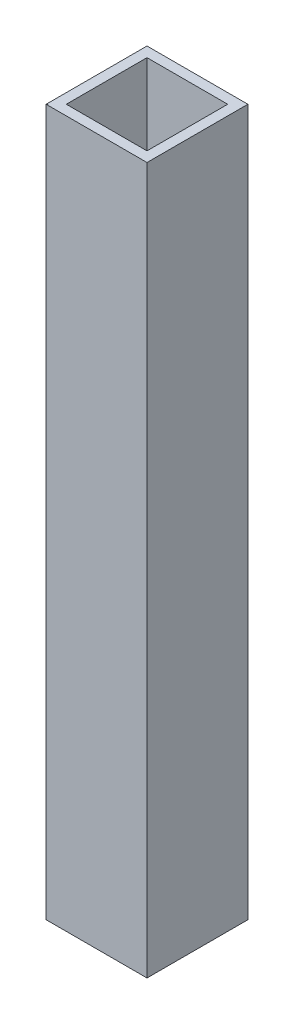
SolidWorks part; units mm, degrees
ref_plane "前视基准面" through (0, 0, 0) normal (0, 0, 1) x (1, 0, 0)
ref_plane "上视基准面" through (0, 0, 0) normal (0, 1, 0) x (1, 0, 0)
ref_plane "右视基准面" through (0, 0, 0) normal (1, 0, 0) x (0, 0, -1)
ref_plane "基准面4" through (0, -70, 0) normal (0, -1, 0) x (1, 0, 0)
sketch "草图1" plane through (0, -70, 0) normal (0, -1, 0) x (1, 0, 0)
  line L0 (5, -5) -> (5, 5)
  line L1 (5, 5) -> (-5, 5)
  line L2 (-5, 5) -> (-5, -5)
  line L3 (-5, -5) -> (5, -5)
  line L4 (-4, 4) -> (4, 4)
  line L5 (4, 4) -> (4, -4)
  line L6 (4, -4) -> (-4, -4)
  line L7 (-4, -4) -> (-4, 4)
extrude "凸台-拉伸1" add sketch "草图1" against normal blind 70
